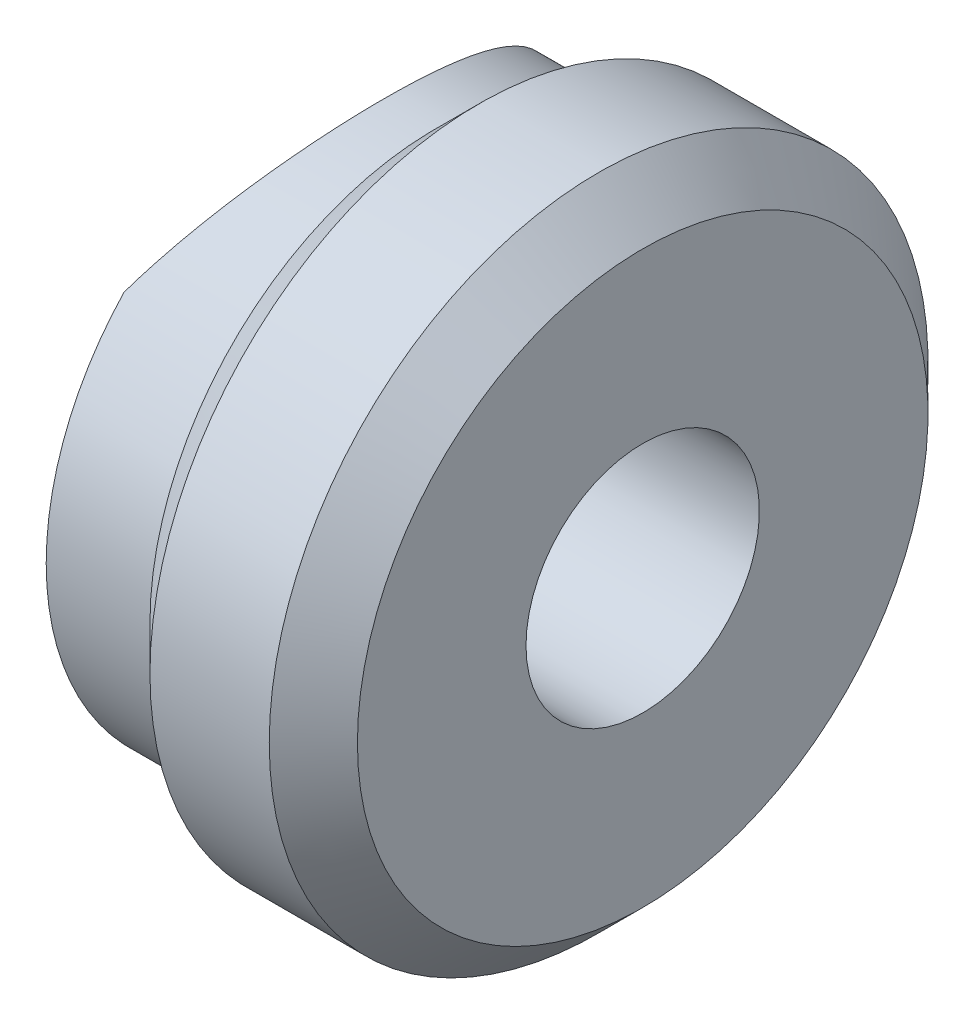
SolidWorks part; units mm, degrees
material "PTFE (geral)"
ref_plane "Plano frontal" through (0, 0, 0) normal (0, 0, 1) x (1, 0, 0)
ref_plane "Plano superior" through (0, 0, 0) normal (0, 1, 0) x (1, 0, 0)
ref_plane "Plano direito" through (0, 0, 0) normal (1, 0, 0) x (0, 0, -1)
sketch "Esboço1" plane through (0, 0, 0) normal (0, 0, 1) x (1, 0, 0)
  line L0 (0, 0) -> (0, 3477.9589) construction
  line L1 (14.2664, 0) -> (3492.2253, 0) construction
  line L2 (0, 5.5) -> (2, 5.5)
  line L3 (2, 5.5) -> (2.85, 6.35)
  line L4 (2.85, 6.35) -> (5.15, 6.35)
  line L5 (5.15, 6.35) -> (6, 5.5)
  line L6 (0, 5.5) -> (0, 2.65)
  line L7 (6, 5.5) -> (6, 2.25)
  line L9 (0, 2.65) -> (0.6928, 2.25)
  line L10 (0.6928, 2.25) -> (6, 2.25)
  dimension "D1" = 4.5
  dimension "D2" = 12.7
  dimension "D3" = 45
  dimension "D4" = 2
  dimension "D5" = 6
  dimension "D6" = 11
  dimension "D7" = 30
  dimension "D8" = 0.4
revolve "Revolução1" add sketch "Esboço1" angle 360 about L1
sketch "Esboço2" plane through (0, 0, 0) normal (0, 1, 0) x (1, 0, 0)
  line L0 (0, 0.0239) -> (0, -0.0239) construction
  circle A0 centre (-7.5, 0) radius 8.5
  point P5 (0, 0)
  dimension "D1" = 17
  dimension "D2" = 7.5
extrude "Corte-extrusão1" cut sketch "Esboço2" against normal through all both and the other way through all
